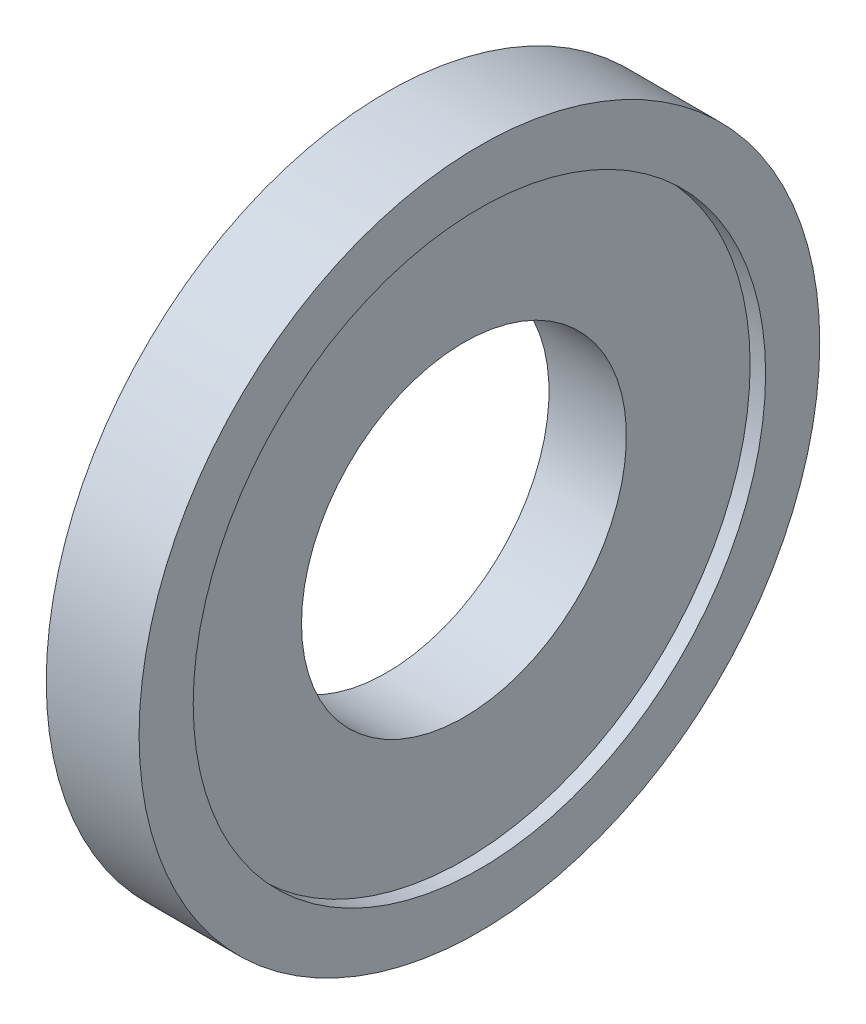
SolidWorks part; units mm, degrees
material "POM 乙缩醛共聚物"
ref_plane "前视基准面" through (0, 0, 0) normal (0, 0, 1) x (1, 0, 0)
ref_plane "上视基准面" through (0, 0, 0) normal (0, 1, 0) x (1, 0, 0)
ref_plane "右视基准面" through (0, 0, 0) normal (1, 0, 0) x (0, 0, -1)
sketch "草图1" plane through (0, 0, 0) normal (0, 0, 1) x (1, 0, 0)
  line L0 (0, 0) -> (4.0926, 0) construction
  line L1 (0, 0) -> (0, 5.25) construction
  line L2 (0, 5.25) -> (0, 11)
  line L3 (0, 11) -> (3, 11)
  line L4 (3, 11) -> (3, 9.25)
  line L5 (3, 9.25) -> (2.5, 9.25)
  line L6 (2.5, 9.25) -> (2.5, 5.25)
  line L7 (2.5, 5.25) -> (0, 5.25)
  dimension "D1" = 22
  dimension "D2" = 10.5
  dimension "D3" = 18.5
  dimension "D4" = 3
  dimension "D5" = 0.5
revolve "旋转1" add sketch "草图1" angle 360 about L0
